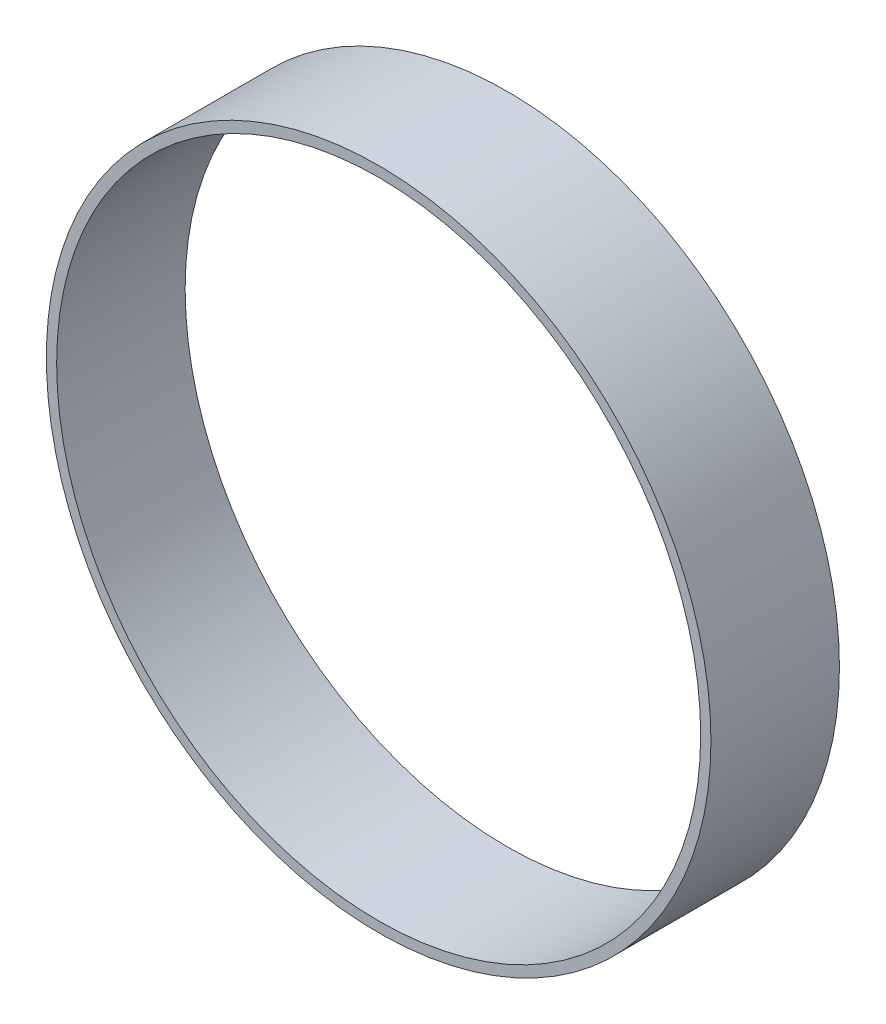
SolidWorks part; units mm, degrees
material "ABS PC"
ref_plane "Front Plane" through (0, 0, 0) normal (0, 0, 1) x (1, 0, 0)
ref_plane "Top Plane" through (0, 0, 0) normal (0, 1, 0) x (1, 0, 0)
ref_plane "Right Plane" through (0, 0, 0) normal (1, 0, 0) x (0, 0, -1)
sketch "Sketch1" plane through (0, 0, 0) normal (0, 0, 1) x (1, 0, 0)
  circle A0 centre (0, 0) radius 16.4211
  circle A1 centre (0, 0) radius 15.9131
  dimension "D1" = 32.8422
  dimension "D2" = 0.508
extrude "Boss-Extrude1" add sketch "Sketch1" along normal blind 6.35
